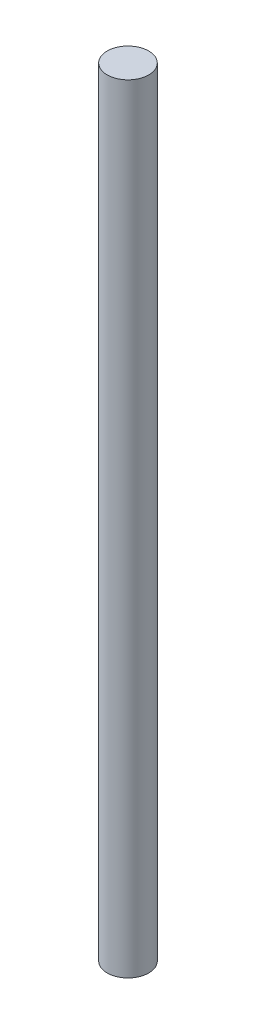
SolidWorks part; units mm, degrees
ref_plane "Front Plane" through (0, 0, 0) normal (0, 0, 1) x (1, 0, 0)
ref_plane "Top Plane" through (0, 0, 0) normal (0, 1, 0) x (1, 0, 0)
ref_plane "Right Plane" through (0, 0, 0) normal (1, 0, 0) x (0, 0, -1)
sketch "Sketch1" plane through (0, 0, 0) normal (0, 1, 0) x (1, 0, 0)
  circle A0 centre (0, 0) radius 2
extrude "Boss-Extrude1" add sketch "Sketch1" along normal blind 75
